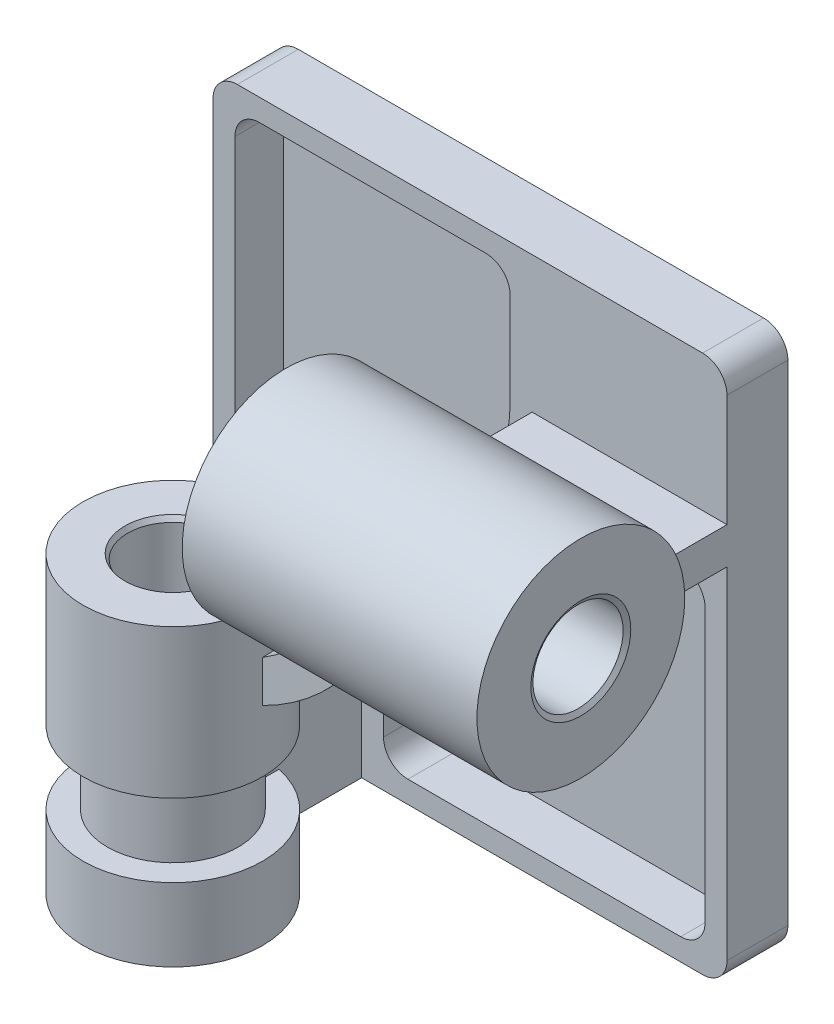
SolidWorks part; units mm, degrees
material "Alloy Steel"
ref_plane "Front Plane" through (0, 0, 0) normal (0, 0, 1) x (1, 0, 0)
ref_plane "Top Plane" through (0, 0, 0) normal (0, 1, 0) x (1, 0, 0)
ref_plane "Right Plane" through (0, 0, 0) normal (1, 0, 0) x (0, 0, -1)
sketch "Sketch1" plane through (0, 0, 0) normal (0, 0, 1) x (1, 0, 0)
  line L1 (10, 0) -> (201, 0)
  line L2 (0, 10) -> (0, 211)
  line L3 (10, 221) -> (201, 221)
  line L4 (211, 10) -> (211, 211)
  arc A0 (10, 0) -> (0, 10) centre (10, 10) cw
  arc A1 (201, 0) -> (211, 10) centre (201, 10) ccw
  arc A2 (201, 221) -> (211, 211) centre (201, 211) cw
  arc A3 (0, 211) -> (10, 221) centre (10, 211) cw
  point P8 (0, 0)
  point P11 (211, 0)
  point P16 (0, 221)
  dimension "D3" = 10
  dimension "D1" = 221
  dimension "D2" = 211
extrude "Boss-Extrude1" add sketch "Sketch1" along normal blind 25
sketch "Sketch5" plane through (0, 0, 25) normal (0, 0, 1) x (1, 0, 0)
  line L0 (46, 0) -> (46, 80)
  line L1 (10, 0) -> (201, 0) construction
  line L2 (131, 165) -> (211, 165)
  line L3 (211, 10) -> (211, 211) construction
  line L4 (61, 0) -> (61, 66.1314)
  line L5 (144.8686, 150) -> (211, 150)
  line L6 (211, 165) -> (211, 150)
  line L7 (61, 0) -> (46, 0)
  arc A0 (46, 80) -> (131, 165) centre (46, 165) ccw
  arc A1 (61, 66.1314) -> (144.8686, 150) centre (46, 165) ccw
  dimension "D2" = 80
  dimension "D3" = 165
  dimension "D1" = 80
  dimension "D4" = 15
extrude "Boss-Extrude3" add sketch "Sketch5" along normal blind 70
ref_plane "Plane1" through (0, -10, 0) normal (0, -1, 0) x (-1, 0, 0)
sketch "Sketch7" plane through (0, -10, 0) normal (0, -1, 0) x (-1, 0, 0)
  line L0 (-10, 0) -> (-201, 0) construction
  line L1 (-46, -95) -> (-46, -25) construction
  circle A0 centre (-53.5, -95) radius 36.8333
  dimension "D1" = 73.6667
  dimension "D2" = 95
  dimension "D3" = 7.5
extrude "Boss-Extrude4" add sketch "Sketch7" against normal blind 121
sketch "Sketch8" plane through (0, -10, 0) normal (0, -1, 0) x (1, 0, 0)
  circle A0 centre (53.5, 95) radius 18.5
  circle A1 centre (53.5, 95) radius 36.8333 construction
  dimension "D1" = 37
extrude "Cut-Extrude2" cut sketch "Sketch8" against normal through all
ref_plane "Plane2" through (221, 0, 0) normal (1, 0, 0) x (0, 0, -1)
sketch "Sketch9" plane through (221, 0, 0) normal (1, 0, 0) x (0, 0, -1)
  line L0 (-95, 150) -> (-95, 165) construction
  circle A0 centre (-95, 157.5) radius 42.6667
  dimension "D1" = 85.3333
extrude "Boss-Extrude5" add sketch "Sketch9" against normal blind 121
sketch "Sketch10" plane through (221, 0, 0) normal (1, 0, 0) x (0, 0, -1)
  circle A0 centre (-95, 157.5) radius 18.5
  circle A1 centre (-95, 157.5) radius 42.6667 construction
  dimension "D1" = 37
extrude "Cut-Extrude3" cut sketch "Sketch10" against normal through all
chamfer "Chamfer1" distance 2 angle 30 4 edges at (100, 157.5, 76.5) (53.5, 111, 76.5) (53.5, -10, 76.5) (221, 157.5, 76.5)
sketch "Sketch11" plane through (0, 0, 25) normal (0, 0, 1) x (1, 0, 0)
  line L0 (192, 141) -> (160.0395, 141)
  line L1 (70, 50.9605) -> (70, 19)
  line L2 (80, 9) -> (192, 9)
  line L3 (202, 19) -> (202, 131)
  arc A0 (77.1429, 60.5437) -> (150.4563, 133.8571) centre (46, 165) ccw
  arc A2 (70, 19) -> (80, 9) centre (80, 19) ccw
  arc A3 (77.1429, 60.5437) -> (70, 50.9605) centre (80, 50.9605) ccw
  arc A6 (192, 141) -> (202, 131) centre (192, 131) cw
  arc A7 (160.0395, 141) -> (150.4563, 133.8571) centre (160.0395, 131) ccw
  arc A8 (192, 9) -> (202, 19) centre (192, 19) ccw
  dimension "D1" = 10
  dimension "D2" = 10
extrude "Cut-Extrude4" cut sketch "Sketch11" against normal offset from surface (20 mm away) 5 up to face at (105.5, 110.5, 0)
sketch "Sketch12" plane through (0, 0, 25) normal (0, 0, 1) x (1, 0, 0)
  line L0 (19, 212) -> (112, 212)
  line L4 (9, 99) -> (9, 202)
  line L6 (201, 221) -> (10, 221) construction
  line L7 (0, 211) -> (0, 10) construction
  line L8 (46, 89) -> (19, 89)
  line L9 (122, 165) -> (122, 202)
  arc A2 (46, 80) -> (131, 165) centre (46, 165) ccw construction
  arc A3 (46, 80) -> (131, 165) centre (46, 165) ccw
  arc A4 (46, 89) -> (122, 165) centre (46, 165) ccw
  arc A5 (19, 89) -> (9, 99) centre (19, 99) cw
  arc A6 (122, 202) -> (112, 212) centre (112, 202) ccw
  arc A7 (19, 212) -> (9, 202) centre (19, 202) ccw
  dimension "D3" = 9
  dimension "D4" = 10
  dimension "D1" = 9
  dimension "D2" = 9
extrude "Cut-Extrude5" cut sketch "Sketch12" against normal offset from surface (20 mm away) 5 contours L0 A6 L9 A4 L8 A5 L4 A7 up to face at (105.5, 110.5, 0)
ref_plane "Plane4" through (0, 20, 0) normal (0, -1, 0) x (-1, 0, 0)
sketch "Sketch16" plane through (0, 20, 0) normal (0, -1, 0) x (-1, 0, 0)
  circle A0 centre (-53.5, -95) radius 26.8333
  circle A1 centre (-53.5, -95) radius 36.8333 construction
  circle A2 centre (-53.5, -95) radius 36.8333
  dimension "D1" = 10
extrude "Cut-Extrude7" cut sketch "Sketch16" against normal blind 30
ref_plane "Plane6" through (0, 0, 25) normal (0, 0, 1) x (1, 0, 0)
sketch "Sketch18" plane through (0, 0, 25) normal (0, 0, 1) x (1, 0, 0)
  line L4 (61, 50) -> (46, 50)
  line L5 (46, 50) -> (46, 20)
  line L6 (46, 20) -> (61, 20)
  line L7 (61, 20) -> (61, 50)
  line L8 (61, 50) -> (46, 50)
  line L9 (46, 50) -> (46, 20)
  line L10 (46, 20) -> (61, 20)
  line L11 (61, 20) -> (61, 50)
  dimension "D1" = 0
extrude "Boss-Extrude7" add sketch "Sketch18" along normal up to surface (44.2361 mm away)
equation "\"A\"= 221"
equation "\"D1@Sketch1\"=\"A\""
equation "\"B\"= 211"
equation "\"D2@Sketch1\"=\"B\""
equation "\"C\"= 165"
equation "\"D\"= 121"
equation "\"E\"= 37"
equation "\"X\"= \"A\" / 3"
equation "\"Y\"= \"B\" / 3 + 15"
equation "\"D3@Sketch5\"=\"C\""
equation "\"D1@Sketch7\"=\"X\""
equation "\"D1@Boss-Extrude4\"=\"D\""
equation "\"D1@Sketch8\"=\"E\""
equation "\"D1@Sketch9\"=\"Y\""
equation "\"D1@Boss-Extrude5\"=\"D\""
equation "\"D1@Sketch10\"=\"E\""
